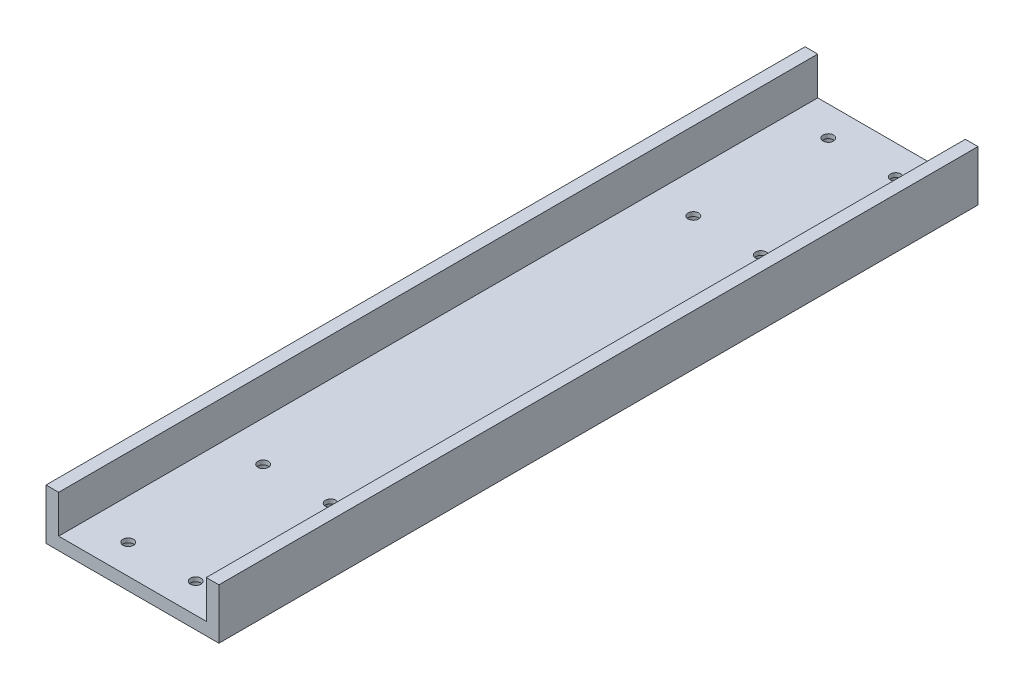
SolidWorks part; units mm, degrees
ref_plane "Front Plane" through (0, 0, 0) normal (0, 0, 1) x (1, 0, 0)
ref_plane "Top Plane" through (0, 0, 0) normal (0, 1, 0) x (1, 0, 0)
ref_plane "Right Plane" through (0, 0, 0) normal (1, 0, 0) x (0, 0, -1)
sketch "Sketch2" plane through (0, 0, 0) normal (0, 0, 1) x (1, 0, 0)
  line L1 (-17.5, 1.5) -> (17.5, 1.5)
  line L2 (-17.5, 1.5) -> (-17.5, -1.5)
  line L3 (-17.5, -1.5) -> (17.5, -1.5)
  line L4 (17.5, 1.5) -> (17.5, -1.5)
  line L5 (-17.5, 1.5) -> (17.5, -1.5) construction
  line L6 (-17.5, -1.5) -> (17.5, 1.5) construction
  line L7 (17.5, -1.5) -> (20.5, -1.5)
  line L8 (17.5, -1.5) -> (17.5, 10.5)
  line L9 (17.5, 10.5) -> (20.5, 10.5)
  line L10 (20.5, -1.5) -> (20.5, 10.5)
  line L11 (-17.5, -1.5) -> (-20.5, -1.5)
  line L12 (-17.5, -1.5) -> (-17.5, 10.5)
  line L13 (-17.5, 10.5) -> (-20.5, 10.5)
  line L14 (-20.5, -1.5) -> (-20.5, 10.5)
  point P0 (0, 0)
  dimension "D1" = 35
  dimension "D2" = 3
  dimension "D3" = 3
  dimension "D4" = 3
  dimension "D5" = 12
  dimension "D6" = 12
extrude "Boss-Extrude1" add sketch "Sketch2" along normal blind 90 contours L7 L10 L9 L8 L4 | L4 L1 L2 L3 | L14 L11 L2 L12 L13
sketch "Sketch3" plane through (0, -1.5, 0) normal (0, -1, 0) x (1, 0, 0)
  line L0 (0, -55) -> (0, 55) construction
  line L2 (-20.5, 0) -> (20.5, 0) construction
  circle A0 centre (-8, 83) radius 1.25
  circle A1 centre (8, 83) radius 1.25
  circle A2 centre (8, 51) radius 1.25
  circle A3 centre (-8, 51) radius 1.25
  dimension "D1" = 2.5
  dimension "D4" = 8
  dimension "D5" = 51
  dimension "D2" = 2
  dimension "D3" = 2
extrude "Cut-Extrude1" cut sketch "Sketch3" against normal through all both and the other way through all
sketch "Sketch4" plane through (0, -1.5, 0) normal (0, -1, 0) x (1, 0, 0)
  line L0 (-8, 83) -> (-8, 51) construction
  circle A0 centre (-8, 83) radius 2.25
  circle A1 centre (8, 83) radius 2.25
  circle A2 centre (8, 51) radius 2.25
  circle A3 centre (-8, 51) radius 2.25
  dimension "D1" = 4.5
  dimension "D4" = 32
  dimension "D2" = 2
  dimension "D3" = 2
extrude "Cut-Extrude2" cut sketch "Sketch4" against normal blind 2
mirror "Mirror1" about plane through (0, 0, 0) normal (0, 0, 1) of "Cut-Extrude1", "Boss-Extrude1", "Cut-Extrude2"
